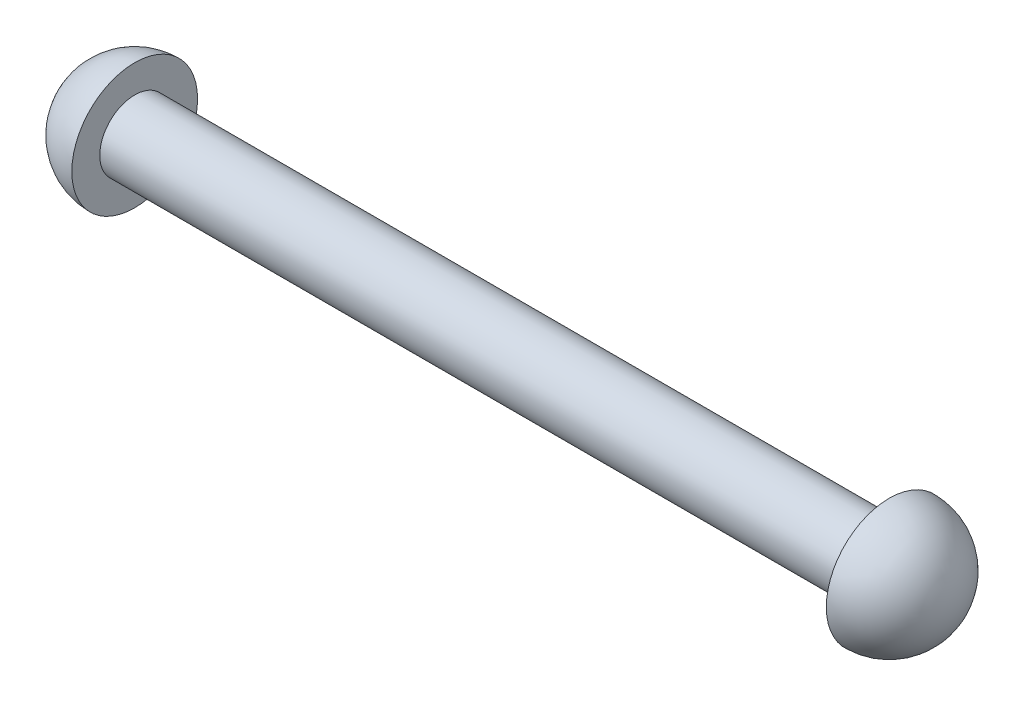
SolidWorks part; units mm, degrees
material "AISI 1020"
ref_plane "Front Plane" through (0, 0, 0) normal (0, 0, 1) x (1, 0, 0)
ref_plane "Top Plane" through (0, 0, 0) normal (0, 1, 0) x (1, 0, 0)
ref_plane "Right Plane" through (0, 0, 0) normal (1, 0, 0) x (0, 0, -1)
sketch "Sketch1" plane through (0, 0, 0) normal (0, 1, 0) x (1, 0, 0)
  line L1 (-34.29, -3.175) -> (34.29, -3.175)
  line L8 (34.29, -3.175) -> (34.29, -5.715)
  line L9 (-40.005, 0) -> (40.005, 0)
  line L10 (-34.29, -3.175) -> (-34.29, -5.715)
  arc A1 (-40.005, 0) -> (-34.29, -5.715) centre (-34.29, 0) ccw
  arc A2 (40.005, 0) -> (34.29, -5.715) centre (34.29, 0) cw
  point P0 (0, 0)
revolve "Revolve1" add sketch "Sketch1" angle 360 about L9
